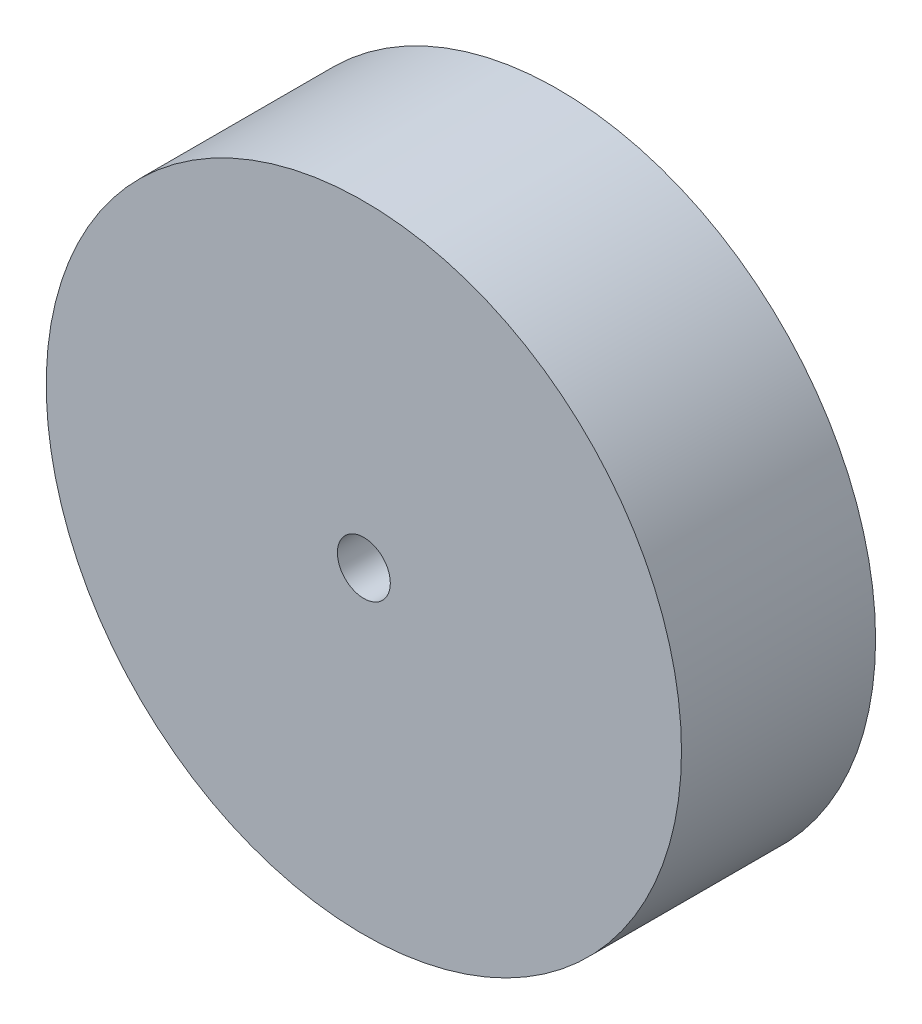
SolidWorks part; units mm, degrees
ref_plane "Front" through (0, 0, 0) normal (0, 0, 1) x (1, 0, 0)
ref_plane "Top" through (0, 0, 0) normal (0, 1, 0) x (1, 0, 0)
ref_plane "Right" through (0, 0, 0) normal (1, 0, 0) x (0, 0, -1)
sketch "Эскиз1" plane through (0, 0, 0) normal (0, 0, 1) x (1, 0, 0)
  circle A0 centre (0, 0) radius 2.75
  dimension "D1" = 5.5
extrude "Бобышка-Вытянуть1" add sketch "Эскиз1" along normal blind 3
sketch "Эскиз2" plane through (0, 0, 3) normal (0, 0, 1) x (1, 0, 0)
  circle A0 centre (0, 0) radius 9
  dimension "D1" = 18
extrude "Бобышка-Вытянуть2" add sketch "Эскиз2" along normal blind 5.5
sketch "Эскиз3" plane through (0, 0, 8.5) normal (0, 0, 1) x (1, 0, 0)
  circle A0 centre (0, 0) radius 0.75
  dimension "D1" = 1.5
extrude "Вырез-Вытянуть1" cut sketch "Эскиз3" against normal blind 7.5
chamfer "Фаска1" distance 0.7 angle 45 1 edges at (0.75, 0, 1)
